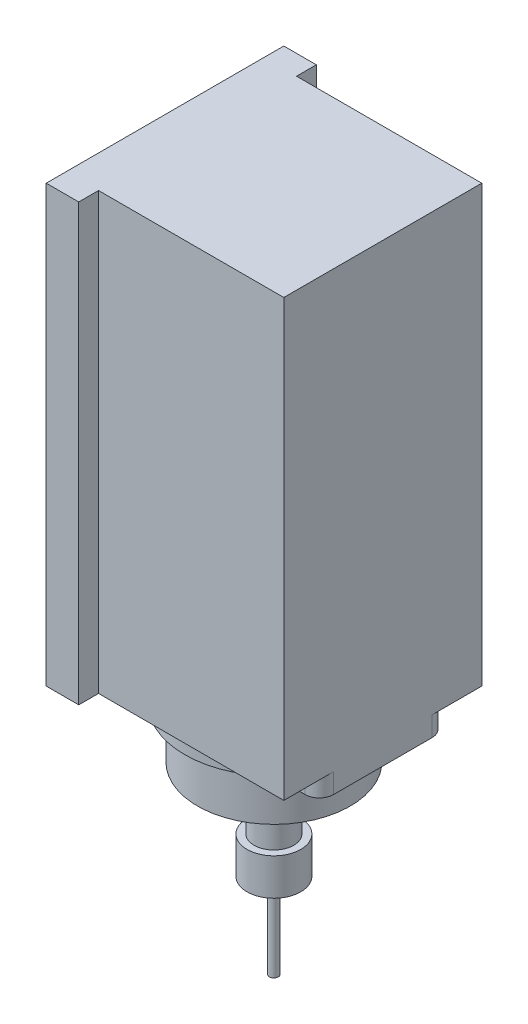
SolidWorks part; units mm, degrees
ref_plane "Front Plane" through (0, 0, 0) normal (0, 0, 1) x (1, 0, 0)
ref_plane "Top Plane" through (0, 0, 0) normal (0, 1, 0) x (1, 0, 0)
ref_plane "Right Plane" through (0, 0, 0) normal (1, 0, 0) x (0, 0, -1)
sketch "Body" plane through (0, 0, 0) normal (0, 1, 0) x (1, 0, 0)
  line L0 (-38.5, -35) -> (-38.5, -42)
  line L2 (38.5, 35) -> (38.5, -35)
  line L4 (-38.5, 35) -> (-38.5, -35)
  line L5 (0, -35) -> (0, 35) construction
  line L6 (38.5, 0) -> (-38.5, 0) construction
  line L7 (-38.5, -42) -> (-27, -42)
  line L8 (-27, -42) -> (-27, -35)
  line L9 (-38.5, 35) -> (-38.5, 42)
  line L10 (-38.5, 42) -> (-27, 42)
  line L11 (-27, 42) -> (-27, 35)
  line L12 (-27, 35) -> (38.5, 35)
  line L13 (-27, -35) -> (38.5, -35)
  point P0 (0, 0)
  dimension "D1" = 70
  dimension "D2" = 77
  dimension "D3" = 7
  dimension "D4" = 11.5
  dimension "D5" = 7
  dimension "D6" = 11.5
extrude "Body_extrud" add sketch "Body" along normal blind 154
sketch "Sketch2" plane through (0, 0, 0) normal (0, -1, 0) x (1, 0, 0)
  line L1 (-33.5, 22.4265) -> (-22.1202, 22.4265)
  line L2 (-38.5, 17.4265) -> (-38.5, -17.4265)
  line L3 (-33.5, -22.4265) -> (-22.1202, -22.4265)
  line L4 (38.5, 17.4265) -> (38.5, -17.4265)
  line L5 (0, -20) -> (0, 20) construction
  line L6 (-38.5, 0) -> (38.5, 0) construction
  line L7 (22.1202, 22.4265) -> (33.5, 22.4265)
  line L8 (22.1202, -22.4265) -> (33.5, -22.4265)
  arc A0 (-22.1202, -22.4265) -> (22.1202, -22.4265) centre (0, 0) ccw
  arc A1 (22.1202, 22.4265) -> (-22.1202, 22.4265) centre (0, 0) ccw
  arc A2 (-38.5, -17.4265) -> (-33.5, -22.4265) centre (-33.5, -17.4265) ccw
  arc A3 (33.5, -22.4265) -> (38.5, -17.4265) centre (33.5, -17.4265) ccw
  arc A4 (33.5, 22.4265) -> (38.5, 17.4265) centre (33.5, 17.4265) cw
  arc A5 (-33.5, 22.4265) -> (-38.5, 17.4265) centre (-33.5, 17.4265) ccw
  point P0 (0, 0)
  dimension "D2" = 63
  dimension "D1" = 5
extrude "Boss-Extrude2" add sketch "Sketch2" along normal blind 7
sketch "Sketch3" plane through (0, -7, 0) normal (0, -1, 0) x (-1, 0, 0)
  circle A0 centre (0, 0) radius 27
  dimension "D1" = 54
extrude "Boss-Extrude3" add sketch "Sketch3" along normal blind 18 contours A0
sketch "Sketch4" plane through (0, -25, 0) normal (0, -1, 0) x (-1, 0, 0)
  circle A0 centre (0, 0) radius 14.5
  dimension "D1" = 29
extrude "Boss-Extrude4" add sketch "Sketch4" along normal blind 3
sketch "Sketch5" plane through (0, -28, 0) normal (0, -1, 0) x (-1, 0, 0)
  circle A0 centre (0, 0) radius 7
  dimension "D1" = 14
extrude "Boss-Extrude5" add sketch "Sketch5" along normal blind 19
sketch "Sketch6" plane through (0, -47, 0) normal (0, -1, 0) x (1, 0, 0)
  circle A0 centre (0, 0) radius 9.5
  dimension "D1" = 19
extrude "Boss-Extrude6" add sketch "Sketch6" along normal blind 13
sketch "Sketch7" plane through (0, -60, 0) normal (0, -1, 0) x (1, 0, 0)
  circle A0 centre (0, 0) radius 1.5875
  dimension "D1" = 3.175
extrude "Boss-Extrude7" add sketch "Sketch7" along normal blind 30
